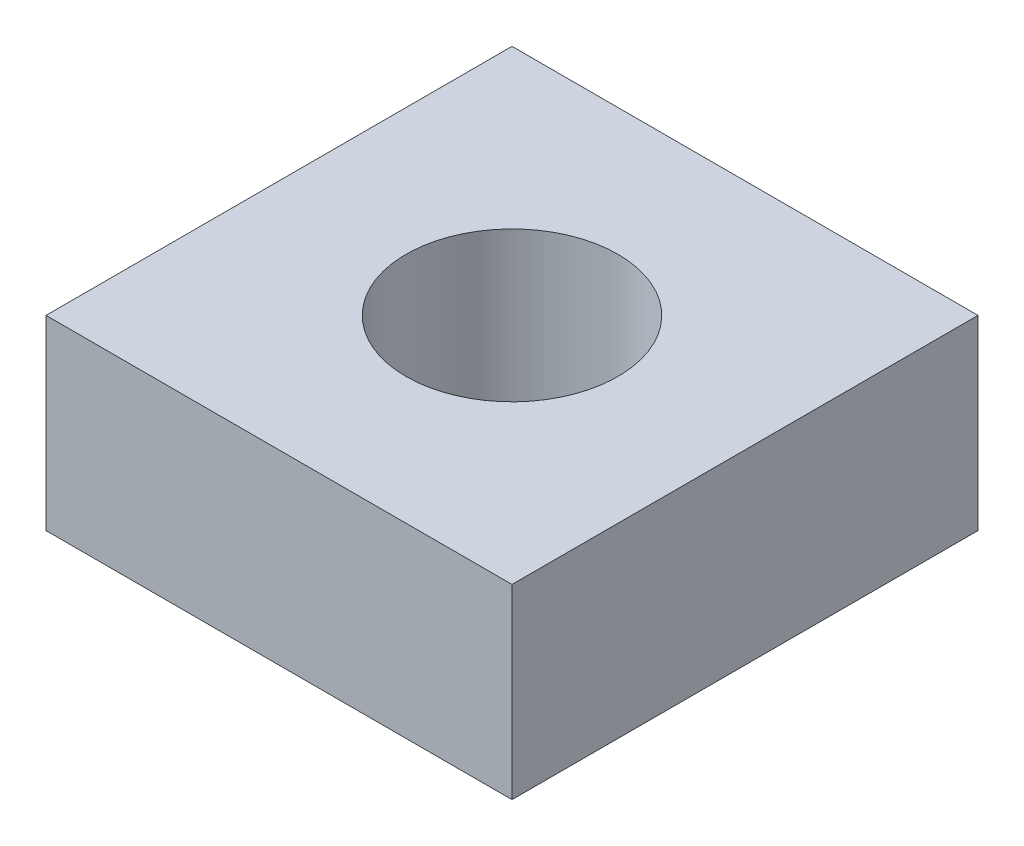
SolidWorks part; units mm, degrees
ref_plane "Front Plane" through (0, 0, 0) normal (0, 0, 1) x (1, 0, 0)
ref_plane "Top Plane" through (0, 0, 0) normal (0, 1, 0) x (1, 0, 0)
ref_plane "Right Plane" through (0, 0, 0) normal (1, 0, 0) x (0, 0, -1)
sketch "Sketch1" plane through (0, 0, 0) normal (0, 1, 0) x (1, 0, 0)
  line L1 (-2.75, 2.75) -> (2.75, 2.75)
  line L2 (-2.75, 2.75) -> (-2.75, -2.75)
  line L3 (-2.75, -2.75) -> (2.75, -2.75)
  line L4 (2.75, 2.75) -> (2.75, -2.75)
  line L5 (-2.75, 2.75) -> (2.75, -2.75) construction
  line L6 (-2.75, -2.75) -> (2.75, 2.75) construction
  point P0 (0, 0)
  dimension "D1" = 5.5
  dimension "D2" = 5.5
extrude "Boss-Extrude1" add sketch "Sketch1" along normal blind 2.2
sketch "Sketch2" plane through (0, 2.2, 0) normal (0, 1, 0) x (1, 0, 0)
  point P0 (0, 0)
hole_wizard "M3x0.5 Tapped Hole1" positions "Sketch2" profile "Sketch3" tap size "M3x0.5" standard "ANSI Metric" end condition through all
sketch "Sketch3" plane through (0, 2.2, 0) normal (1, 0, 0) x (0, 0, 1)
  line L0 (0, 0) -> (0, 2.2)
  line L1 (0, 2.2) -> (1.25, 2.2)
  line L2 (1.25, 2.2) -> (1.25, 0)
  line L5 (1.25, 0) -> (0, 0)
  line L11 (0, -6.35) -> (0, 107.95) construction
  dimension "Thru Tap Drill Dia." = 2.5
  dimension "Thru Tap Drill Depth" = 2.2
cosmetic thread "Hole Thread1" parameters "D2"=3
